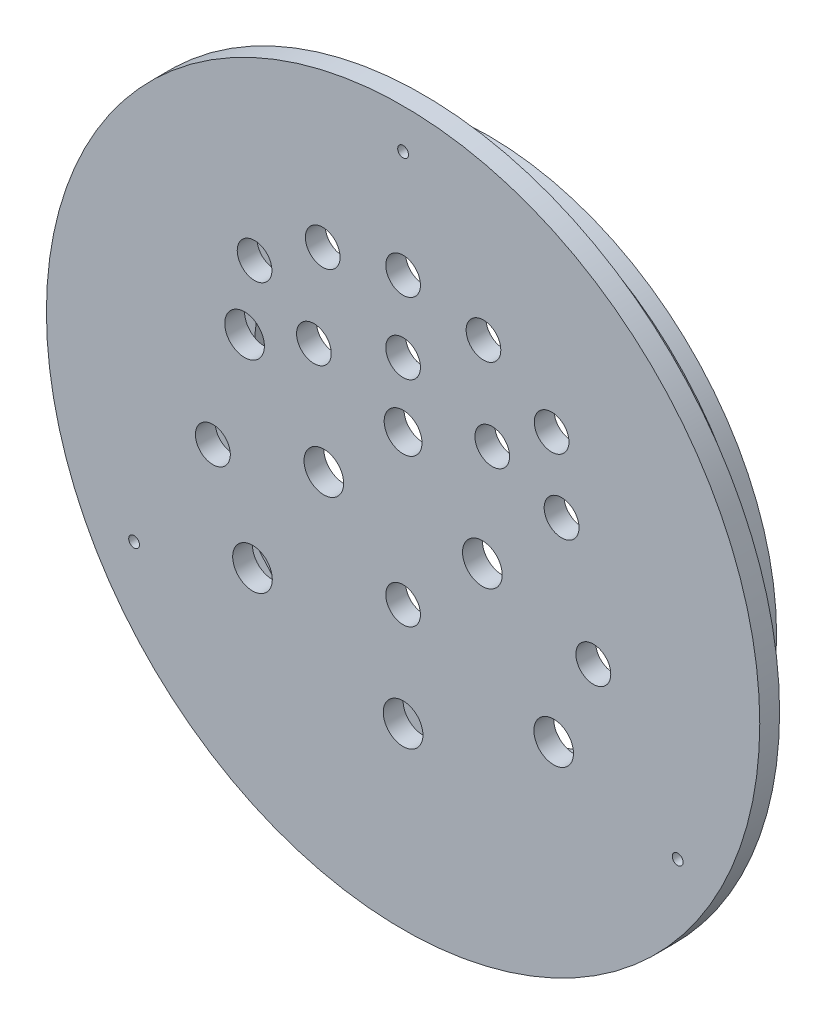
SolidWorks part; units mm, degrees
material "6061-T6 (SS)"
ref_plane "Front Plane" through (0, 0, 0) normal (0, 0, 1) x (1, 0, 0)
ref_plane "Top Plane" through (0, 0, 0) normal (0, 1, 0) x (1, 0, 0)
ref_plane "Right Plane" through (0, 0, 0) normal (1, 0, 0) x (0, 0, -1)
sketch "Sketch1" plane through (0, 0, 0) normal (0, 0, 1) x (1, 0, 0)
  circle A0 centre (0, 0) radius 114.3
  dimension "D1" = 228.6
extrude "Extrude1" add sketch "Sketch1" along normal blind 6.35
sketch "Sketch2" plane through (0, 0, 0) normal (0, 0, -1) x (-1, 0, 0)
  circle A0 centre (0, 0) radius 93.6625
  dimension "D1" = 187.325
extrude "Extrude2" add sketch "Sketch2" along normal blind 15.875
sketch "Sketch3" plane through (0, 0, -15.875) normal (0, 0, -1) x (-1, 0, 0)
  circle A0 centre (0, 0) radius 87.3125
  dimension "D1" = 174.625
extrude "Cut-Extrude1" cut sketch "Sketch3" against normal blind 15.875
sketch "Sketch4" plane through (0, 0, 0) normal (1, 0, 0) x (0, 0, -1)
  line L0 (15.875, 93.6625) -> (0, 93.6625) construction
  line L1 (2.8084, 93.6625) -> (5.9834, 93.6625)
  line L2 (2.8084, 93.6625) -> (2.8084, 91.1225)
  line L3 (2.8084, 91.1225) -> (5.9834, 91.1225)
  line L4 (5.9834, 93.6625) -> (5.9834, 91.1225)
  line L5 (0, 0) -> (42.3826, 0) construction
  line L6 (8.6645, 93.6625) -> (11.8395, 93.6625)
  line L7 (8.6645, 93.6625) -> (8.6645, 91.1225)
  line L8 (8.6645, 91.1225) -> (11.8395, 91.1225)
  line L9 (11.8395, 93.6625) -> (11.8395, 91.1225)
  line L10 (0, -114.3) -> (0, 114.3) construction
  dimension "D1" = 2.54
  dimension "D2" = 3.175
  dimension "D3" = 2.8084
  dimension "D4" = 2.6811
revolve "Cut-Revolve1" cut sketch "Sketch4" angle 360 about L5
chamfer "Chamfer1" distance 1.27 angle 45 1 edges at (-93.6625, 0, -15.875)
chamfer "Chamfer2" distance 0.635 angle 45 4 edges at (93.6625, 0, -2.8084) (93.6625, 0, -5.9834) (93.6625, 0, -8.6645) (93.6625, 0, -11.8395)
sketch "Sketch9" plane through (0, 0, 6.35) normal (0, 0, 1) x (1, 0, 0)
  line L0 (0, 0) -> (0, -163.6527) construction
  circle A0 centre (-48.26, -38.1) radius 6.35
  circle A1 centre (48.26, -38.1) radius 6.35
  dimension "D1" = 12.7
  dimension "D2" = 38.1
  dimension "D3" = 48.26
extrude "Cut-Extrude2" cut sketch "Sketch9" against normal through all
sketch "Sketch11" plane through (0, 0, 6.35) normal (0, 0, 1) x (1, 0, 0)
  line L0 (0, 0) -> (47.5954, 47.5954) construction
  line L1 (0, 0) -> (0, 67.31) construction
  line L2 (0, 0) -> (25.7584, 62.1863) construction
  circle A0 centre (0, 0) radius 67.31 construction
  circle A1 centre (25.7584, 62.1863) radius 5.5562
  circle A2 centre (47.5954, 47.5954) radius 5.5562
  circle A3 centre (-47.5954, 47.5954) radius 5.5562
  circle A4 centre (-25.7584, 62.1863) radius 5.5562
  circle A5 centre (0, 67.31) radius 5.5562
  point P8 (0, 0)
  dimension "D1" = 11.1125
  dimension "D3" = 67.31
  dimension "D2" = 11.1125
  dimension "D6" = 11.1125
  dimension "D4" = 45
  dimension "D5" = 22.5
extrude "Cut-Extrude4" cut sketch "Sketch11" against normal through all
sketch "Sketch12" plane through (0, 0, 6.35) normal (0, 0, 1) x (1, 0, 0)
  line L0 (0, 0) -> (0, 104.2553) construction
  circle A0 centre (0, -57.15) radius 6.35
  circle A1 centre (-25.4, 0) radius 6.35
  circle A2 centre (25.4, 0) radius 6.35
  dimension "D1" = 12.7
  dimension "D3" = 12.7
  dimension "D2" = 57.15
  dimension "D4" = 57.15
  dimension "D5" = 25.4
extrude "Cut-Extrude5" cut sketch "Sketch12" against normal through all
sketch "Sketch13" plane through (0, 0, 6.35) normal (0, 0, 1) x (1, 0, 0)
  line L0 (0, 0) -> (0, 44.45) construction
  line L1 (0, 0) -> (28.5719, 34.0507) construction
  circle A0 centre (0, 44.45) radius 5.5563
  circle A1 centre (28.5719, 34.0507) radius 5.5563
  circle A2 centre (-28.5719, 34.0507) radius 5.5563
  point P6 (0, 0)
  dimension "D1" = 11.1125
  dimension "D3" = 44.45
  dimension "D4" = 40
  dimension "D2" = 2
extrude "Cut-Extrude6" cut sketch "Sketch13" against normal through all
sketch "Sketch17" plane through (0, 0, -15.875) normal (0, 0, -1) x (-1, 0, 0)
  circle A0 centre (0, 0) radius 92.3925
  circle A1 centre (0, 0) radius 69.85
  dimension "D1" = 139.7
extrude "Boss-Extrude1" add sketch "Sketch17" along normal blind 5.08
hole_wizard "#12-24 Tapped Hole1" positions "Sketch21" profile "Sketch20" tap size "#12-24" standard "ANSI Inch"
sketch "Sketch21" plane through (0, 0, -20.955) normal (0, 0, -1) x (-1, 0, 0)
  circle A0 centre (0, 0) radius 79.375 construction
  point P5 (0, 79.375)
  point P7 (-79.375, 0)
  point P9 (0, -79.375)
  point P11 (79.375, 0)
  dimension "D1" = 158.75
sketch "Sketch20" plane through (0, 79.375, -20.955) normal (1, 0, 0) x (0, 1, 0)
  line L0 (0, 0) -> (0, 14.224)
  line L1 (0, 14.224) -> (2.2479, 14.224)
  line L2 (2.2479, 14.224) -> (2.2479, 0)
  line L5 (2.2479, 0) -> (0, 0)
  line L10 (0, 14.224) -> (-2.2479, 14.224) construction
  line L11 (0, -6.35) -> (0, 107.95) construction
  dimension "Tap Drill Dia." = 4.4958
  dimension "Tap Drill Depth" = 14.224
  dimension "Drill Angle" = 180
cosmetic thread "Hole Thread9" parameters "D1"=5.08, "D2"=5.4864
cosmetic thread "Hole Thread10" parameters "D1"=5.08, "D2"=5.4864
cosmetic thread "Hole Thread11" parameters "D1"=5.08, "D2"=5.4864
cosmetic thread "Hole Thread12" parameters "D1"=5.08, "D2"=5.4864
hole_wizard "#8-32 Tapped Hole1" positions "Sketch23" profile "Sketch22" tap size "#8-32" standard "ANSI Inch"
sketch "Sketch23" plane through (0, 0, 6.35) normal (0, 0, 1) x (1, 0, 0)
  line L0 (0, 0) -> (0, 101.6) construction
  line L2 (0, 0) -> (-86.2081, -49.7723) construction
  line L4 (87.9882, -50.8) -> (0, 0) construction
  circle A0 centre (0, 0) radius 101.6
  point P0 (0, 101.6)
  point P2 (-86.2081, -49.7723)
  point P4 (87.9882, -50.8)
  dimension "D3" = 203.2
  dimension "D1" = 120
  dimension "D2" = 120
sketch "Sketch22" plane through (0, 101.6, 6.35) normal (1, 0, 0) x (0, -1, 0)
  line L0 (0, 0) -> (0, 10.668)
  line L1 (0, 10.668) -> (1.7272, 10.668)
  line L2 (1.7272, 10.668) -> (1.7272, 0)
  line L5 (1.7272, 0) -> (0, 0)
  line L10 (0, 10.668) -> (-1.7272, 10.668) construction
  line L11 (0, -6.35) -> (0, 107.95) construction
  dimension "Tap Drill Dia." = 3.4544
  dimension "Tap Drill Depth" = 10.668
  dimension "Drill Angle" = 180
cosmetic thread "Hole Thread13" parameters "D1"=6.35, "D2"=4.1656
cosmetic thread "Hole Thread14" parameters "D1"=6.35, "D2"=4.1656
cosmetic thread "Hole Thread15" parameters "D1"=6.35, "D2"=4.1656
sketch "Sketch25" plane through (0, 0, 6.35) normal (0, 0, 1) x (1, 0, 0)
  line L0 (0, 0) -> (0, 26.3324) construction
  circle A0 centre (60.96, -10.16) radius 5.588
  circle A1 centre (-60.96, -10.16) radius 5.588
  dimension "D1" = 11.176
  dimension "D2" = 60.96
  dimension "D3" = 10.16
extrude "Cut-Extrude8" cut sketch "Sketch25" against normal through all
sketch "Sketch24" plane through (0, 0, 0) normal (0, 0, -1) x (-1, 0, 0)
  circle A0 centre (50.8, 25.4) radius 6.35
  dimension "D1" = 12.7
  dimension "D2" = 25.4
  dimension "D3" = 50.8
extrude "Cut-Extrude7" cut sketch "Sketch24" against normal through all
sketch "Sketch26" plane through (0, 0, 6.35) normal (0, 0, 1) x (1, 0, 0)
  line L0 (-50.8, 25.4) -> (50.8, 25.4) construction
  circle A0 centre (50.8, 25.4) radius 5.588
  point P4 (0, 25.4)
  dimension "D1" = 11.176
extrude "Cut-Extrude9" cut sketch "Sketch26" against normal through all
sketch "Sketch27" plane through (0, 0, 6.35) normal (0, 0, 1) x (1, 0, 0)
  line L0 (-48.26, -38.1) -> (48.26, -38.1) construction
  circle A0 centre (0, -24.13) radius 5.5563
  point P6 (0, -38.1)
  dimension "D1" = 11.1125
  dimension "D2" = 13.97
extrude "Cut-Extrude10" cut sketch "Sketch27" against normal through all
sketch "Sketch28" plane through (0, 0, 6.35) normal (0, 0, 1) x (1, 0, 0)
  circle A0 centre (0, 23.7878) radius 6.0626
extrude "Cut-Extrude11" cut sketch "Sketch28" against normal through all
